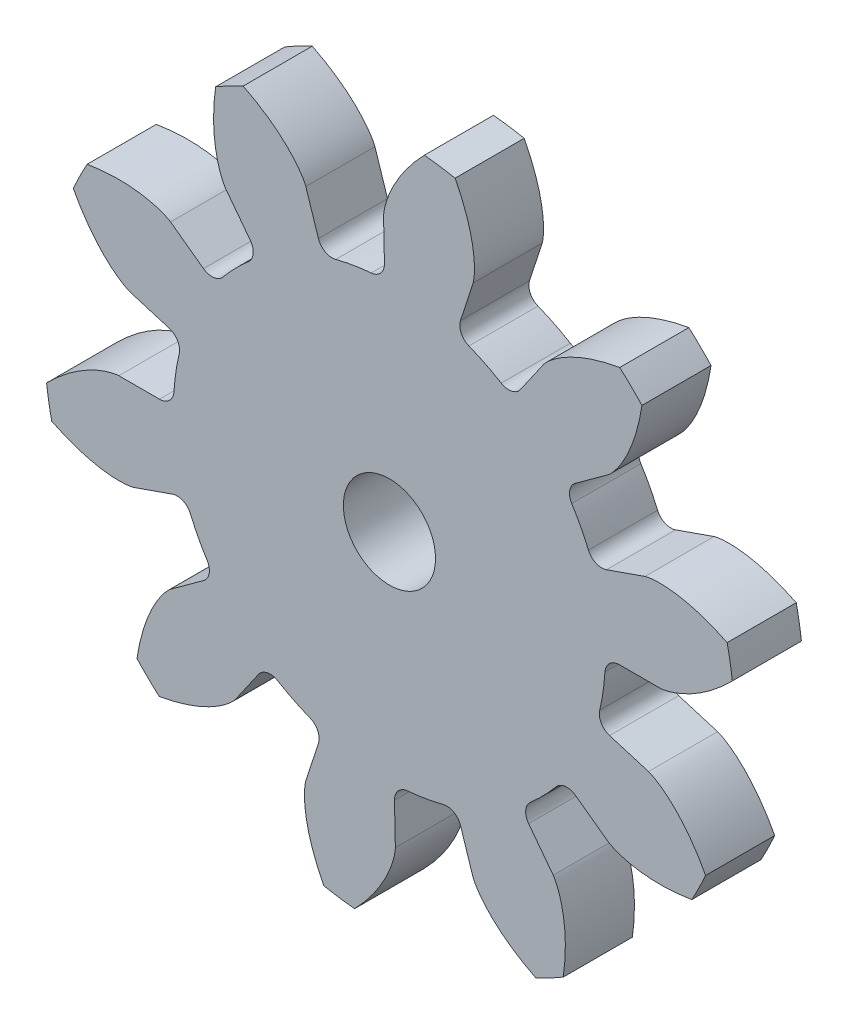
SolidWorks part; units mm, degrees
ref_plane "Front Plane" through (0, 0, 0) normal (0, 0, 1) x (1, 0, 0)
ref_plane "Top Plane" through (0, 0, 0) normal (0, 1, 0) x (1, 0, 0)
ref_plane "Right Plane" through (0, 0, 0) normal (1, 0, 0) x (0, 0, -1)
sketch "Sketch1" plane through (0, 0, 0) normal (0, 0, 1) x (1, 0, 0)
  line L0 (11.7462, 0) -> (9.375, 0)
  line L1 (14.7889, 2.5079) -> (-14.7889, -2.5079)
  line L2 (0, 0) -> (12.4986, 0.1863) construction
  circle A0 centre (0, 0) radius 11.7462 construction
  circle A1 centre (0, 0) radius 15
  circle A2 centre (0, 0) radius 9.375
  circle A3 centre (0, 0) radius 12.5 construction
  spline S0 degree 4 poles (11.7462, 0) (11.7548, 0.0002) (11.7792, 0.0013) (11.8251, 0.0056) (11.8997, 0.0157) (11.9942, 0.0334) (12.1154, 0.0615) (12.2568, 0.1013) (12.4106, 0.1522) (12.5757, 0.215) (12.7384, 0.2842) (12.8986, 0.3593) (13.0561, 0.4395) (13.2442, 0.5429) (13.4661, 0.6756) (13.7194, 0.8429) (13.9992, 1.0471) (14.2756, 1.27) (14.5402, 1.5014) (14.7983, 1.7485) (15.0415, 1.9969) (15.284, 2.2678) (15.5027, 2.5246) (15.7358, 2.8258) (15.9205, 3.0729) (16.1508, 3.4126) (16.2828, 3.6172) (16.4326, 3.8613) (16.4966, 3.972) (16.5361, 4.0402) knots 0 0 0 0 0 0.005377 0.015084 0.028532 0.04661 0.064855 0.092111 0.119476 0.146842 0.174209 0.201575 0.228941 0.256307 0.307035 0.361767 0.4165 0.471232 0.525964 0.580697 0.635429 0.690161 0.744894 0.799626 0.854358 0.909091 0.954545 1 1 1 1 1 construction
  spline S1 degree 4 poles (11.7462, 0) (11.7548, 0.0002) (11.7792, 0.0013) (11.8251, 0.0056) (11.8997, 0.0157) (11.9942, 0.0334) (12.1154, 0.0615) (12.2568, 0.1013) (12.4106, 0.1522) (12.5757, 0.215) (12.7384, 0.2842) (12.8986, 0.3593) (13.0561, 0.4395) (13.2442, 0.5429) (13.4661, 0.6756) (13.7194, 0.8429) (13.9992, 1.0471) (14.2756, 1.27) (14.5402, 1.5014) (14.7983, 1.7485) (15.0415, 1.9969) (15.284, 2.2678) (15.5027, 2.5246) (15.7358, 2.8258) (15.9205, 3.0729) (16.1009, 3.3389) (16.1871, 3.47) (16.2305, 3.5376) knots 0 0 0 0 0 0.005377 0.015084 0.028532 0.04661 0.064855 0.092111 0.119476 0.146842 0.174209 0.201575 0.228941 0.256307 0.307035 0.361767 0.4165 0.471232 0.525964 0.580697 0.635429 0.690161 0.744894 0.799626 0.854358 0.909091 0.909091 0.909091 0.909091 0.909091
  dimension "D1" = 23.4923
  dimension "D2" = 30
  dimension "D3" = 18.75
  dimension "D5" = 25
  dimension "D4" = 8.771
extrude "Boss-Extrude3" add sketch "Sketch1" along normal blind 3 contours L1 A2 | A2 L1 | L0 S1 A1 L1 A2
mirror "Mirror2" about plane through (0, 0, 3) normal (0.1672, -0.9859, 0) of "Boss-Extrude3"
fillet "Fillet1" radius 0.625 2 edges at (8.8509, 3.0908, 1.5) (9.375, 0, 1.5)
pattern_circular "CirPattern8" count 10 over 360 about axis through (0, 0, 3) along (0, 0, -1) of "Boss-Extrude3", "Mirror2", "Fillet1"
sketch "Sketch3" plane through (0, 0, 3) normal (0, 0, 1) x (1, 0, 0)
  circle A0 centre (0, 0) radius 2
  dimension "D1" = 4
extrude "Cut-Extrude2" cut sketch "Sketch3" against normal through all
equation "\"d\" = 25mm'Pitch diameter"
equation "\"N\"= 10'Number of teeth"
equation "\"bl\"= 0.1mm'Backlash"
equation "\"pa\"= 20deg'Pressure angle (deg)"
equation "\"pc\"= ( 3.1415 * \"d\" ) / \"N\"\t'Circular pitch"
equation "\"m\"= \"d\" / \"N\"\t\t\t'module"
equation "\"P\"= \"N\" / \"d\"\t\t\t'Diametral pitch"
equation "\"a\"= 1/\"P\"\t\t\t'Addendum distance"
equation "\"b\"= 1.25 / \"P\"'Dedendum distance"
equation "\"rb\"= (\"d\"/2)*cos(\"pa\")\t\t'base circle radius"
equation "\"cp\"= 3.1415/\"P\"\t\t'Circular pitch"
equation "\"t\"= ( \"cp\" / 2 ) - \"bl\"'tooth tickness"
equation "\"c\"=\"b\"-\"a\"\t\t\t'Clearance"
equation "\"facewidth\"= 3mm'face width"
equation "\"rbd\"= \"rb\" * 2'base circle diameter"
equation "\"D1@Sketch1\"=\"rbd\""
equation "\"D2@Sketch1\"= \"d\" + (\"a\" * 2)"
equation "\"D3@Sketch1\" = \"ded\""
equation "\"D4@Sketch1\"= ((\"t\" /2) / (\"d\"/2)) * (180/3.1415)"
equation "\"D1@Boss-Extrude3\"=\"facewidth\""
equation "\"D1@Fillet1\"=\"c\""
equation "\"D1@CirPattern8\"=\"N\""
equation "\"D5@Sketch1\"=\"d\""
equation "\"ded1\"= \"d\" - 2 * ( ( ( \"d\" / 2 ) - \"rb\" ) + ( 0.5 * ( 1.25 / \"P\" ) ) )"
equation "\"ded2\"= \"d\" - ( \"b\" * 2 )"
equation "\"ded\"= IIF ( \"rb\" < ( \"ded2\" / 2 ) , \"ded1\" , \"ded2\" )"
equation "\"shaftdia\"= 4mm"
equation "\"D1@Sketch3\"=\"shaftdia\""
